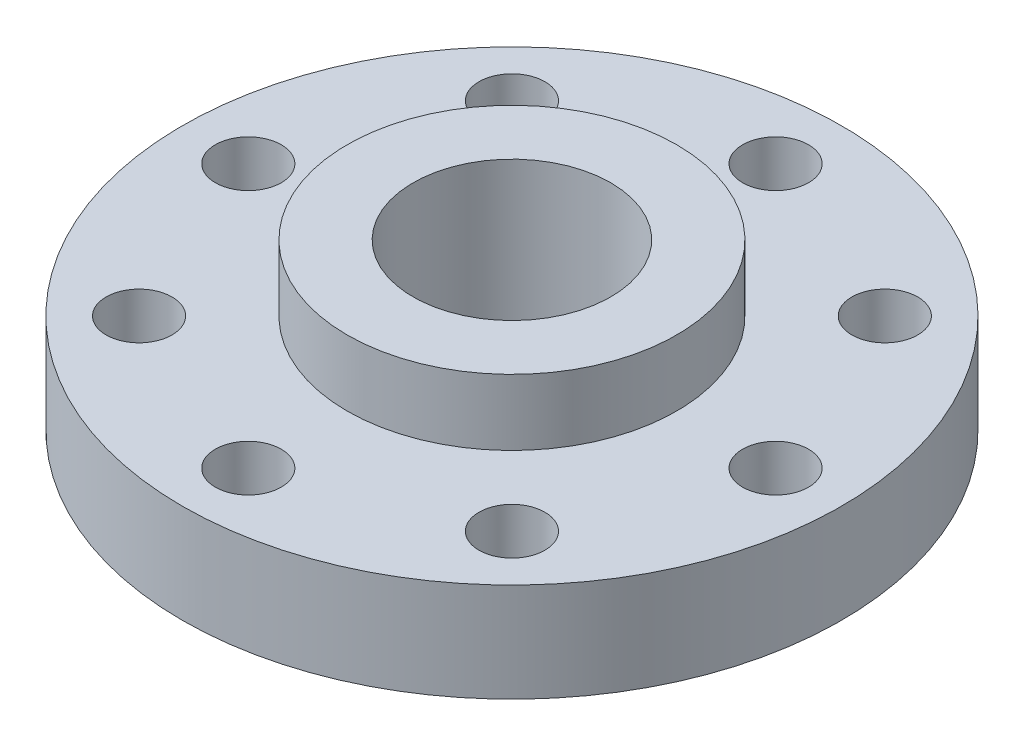
SolidWorks part; units mm, degrees
ref_plane "前视基准面" through (0, 0, 0) normal (0, 0, 1) x (1, 0, 0)
ref_plane "上视基准面" through (0, 0, 0) normal (0, 1, 0) x (1, 0, 0)
ref_plane "右视基准面" through (0, 0, 0) normal (1, 0, 0) x (0, 0, -1)
sketch "草图1" plane through (0, 0, 0) normal (0, 1, 0) x (1, 0, 0)
  circle A0 centre (0, 0) radius 10
  dimension "D1" = 20
extrude "凸台-拉伸1" add sketch "草图1" along normal blind 3
sketch "草图2" plane through (0, 3, 0) normal (0, 1, 0) x (1, 0, 0)
  circle A0 centre (0, 0) radius 5
  dimension "D1" = 10
extrude "凸台-拉伸2" add sketch "草图2" along normal blind 2
sketch "草图3" plane through (0, 0, 0) normal (0, -1, 0) x (1, 0, 0)
  circle A0 centre (0, 0) radius 3
  circle A1 centre (0, 8) radius 1
  circle A2 centre (5.6569, 5.6569) radius 1
  circle A3 centre (8, 0) radius 1
  circle A4 centre (5.6569, -5.6569) radius 1
  circle A5 centre (0, -8) radius 1
  circle A6 centre (-5.6569, -5.6569) radius 1
  circle A7 centre (-8, 0) radius 1
  circle A8 centre (-5.6569, 5.6569) radius 1
  point P22 (0, 0)
  dimension "D1" = 6
  dimension "D2" = 2
  dimension "D4" = 16
  dimension "D3" = 8
extrude "切除-拉伸1" cut sketch "草图3" against normal through all
